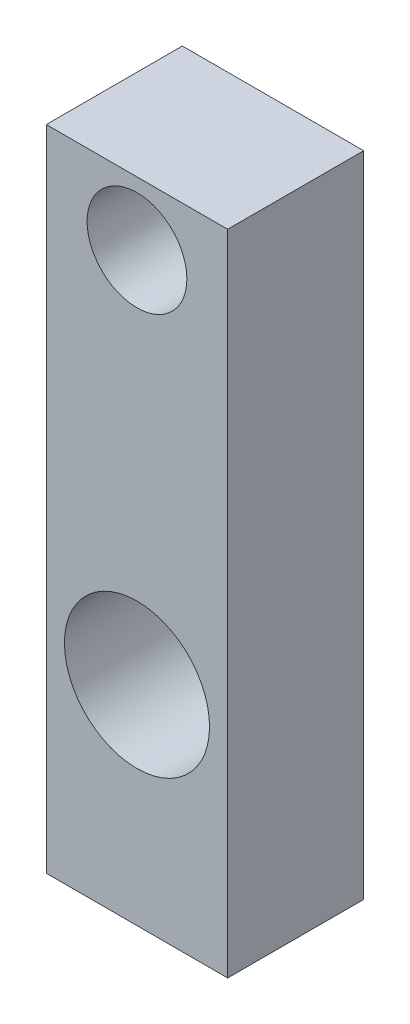
SolidWorks part; units mm, degrees
material "Alliage 1060"
ref_plane "Plan de face" through (0, 0, 0) normal (0, 0, 1) x (1, 0, 0)
ref_plane "Plan de dessus" through (0, 0, 0) normal (0, 1, 0) x (1, 0, 0)
ref_plane "Plan de droite" through (0, 0, 0) normal (1, 0, 0) x (0, 0, -1)
sketch "Esquisse1" plane through (0, 0, 0) normal (0, 0, 1) x (1, 0, 0)
  line L0 (0, 66) -> (40, 26) construction
  line L1 (0, 0) -> (40, 0)
  line L2 (0, 0) -> (0, 143)
  line L3 (0, 143) -> (40, 143)
  line L4 (40, 0) -> (40, 143)
  line L5 (20, 143) -> (20, 0) construction
  circle A0 centre (20, 46) radius 16
  circle A1 centre (20, 129) radius 11
  point P5 (20, 46)
  dimension "D3" = 32
  dimension "D7" = 22
  dimension "D1" = 46
  dimension "D2" = 40
  dimension "D4" = 45
  dimension "D5" = 143
  dimension "D6" = 14
extrude "Boss.-Extru.1" add sketch "Esquisse1" along normal blind 30
